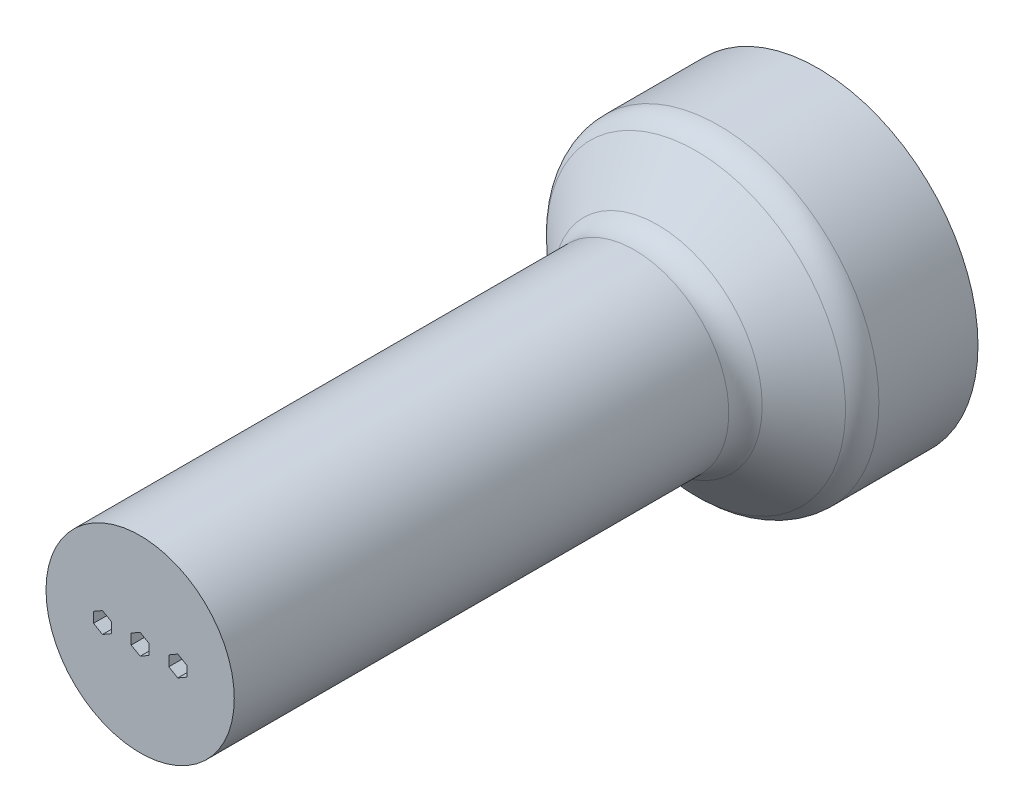
SolidWorks part; units mm, degrees
ref_plane "Front Plane" through (0, 0, 0) normal (0, 0, 1) x (1, 0, 0)
ref_plane "Top Plane" through (0, 0, 0) normal (0, 1, 0) x (1, 0, 0)
ref_plane "Right Plane" through (0, 0, 0) normal (1, 0, 0) x (0, 0, -1)
sketch "Sketch1" plane through (0, 0, 0) normal (0, 0, 1) x (1, 0, 0)
  circle A0 centre (0, 0) radius 25
  dimension "D1" = 50
extrude "Boss-Extrude1" add sketch "Sketch1" along normal blind 150
sketch "Sketch2" plane through (0, 0, 0) normal (0, 0, 1) x (1, 0, 0)
  circle A0 centre (0, 0) radius 42.5
  point P0 (0, 0)
  dimension "D1" = 85
extrude "Boss-Extrude2" add sketch "Sketch2" against normal blind 30 contours A0
sketch "Sketch3" plane through (0, 0, 0) normal (0, 1, 0) x (1, 0, 0)
  line L0 (0, 0) -> (0, -277.5288) construction
  line L1 (25, 0) -> (25, -15)
  line L2 (25, 0) -> (42.5, 0)
  line L3 (42.5, 0) -> (25, -15)
  dimension "D2" = 15
revolve "Revolve1" add sketch "Sketch3" angle 360 about L0
fillet "Fillet4" radius 8 1 edges at (-25, 0, 15)
fillet "Fillet5" radius 8 1 edges at (42.5, 0, 0)
sketch "Sketch4" plane through (0, 0, 0) normal (0, 0, 1) x (1, 0, 0)
  line L0 (0, 0) -> (-67.4265, 0) construction
  line L1 (-67.4265, 0) -> (67.201, 0) construction
  circle A0 centre (0, 0) radius 1.6
  circle A1 centre (-10, 0) radius 1.6
  circle A2 centre (10, 0) radius 1.6
  dimension "D1" = 3.2
  dimension "D2" = 10
  dimension "D3" = 10
extrude "Cut-Extrude1" cut sketch "Sketch4" against normal up to surface (30 mm away) up to face at (42.5, 0, -30)
sketch "Sketch5" plane through (0, 0, 150) normal (0, 0, 1) x (1, 0, 0)
  line L1 (-7.6184, -1.375) -> (-7.6184, 1.375)
  line L2 (-7.6184, 1.375) -> (-10, 2.75)
  line L3 (-10, 2.75) -> (-12.3816, 1.375)
  line L4 (-12.3816, 1.375) -> (-12.3816, -1.375)
  line L5 (-12.3816, -1.375) -> (-10, -2.75)
  line L6 (-10, -2.75) -> (-7.6184, -1.375)
  line L7 (0, -2.75) -> (2.3816, -1.375)
  line L8 (2.3816, -1.375) -> (2.3816, 1.375)
  line L9 (2.3816, 1.375) -> (0, 2.75)
  line L10 (0, 2.75) -> (-2.3816, 1.375)
  line L11 (-2.3816, 1.375) -> (-2.3816, -1.375)
  line L12 (-2.3816, -1.375) -> (0, -2.75)
  line L13 (10, -2.75) -> (12.3816, -1.375)
  line L14 (12.3816, -1.375) -> (12.3816, 1.375)
  line L15 (12.3816, 1.375) -> (10, 2.75)
  line L16 (10, 2.75) -> (7.6184, 1.375)
  line L17 (7.6184, 1.375) -> (7.6184, -1.375)
  line L18 (7.6184, -1.375) -> (10, -2.75)
  circle A0 centre (-10, 0) radius 1.6 construction
  circle A1 centre (0, 0) radius 1.6 construction
  circle A2 centre (10, 0) radius 1.6 construction
  circle A3 centre (-10, 0) radius 1.6
  circle A4 centre (0, 0) radius 1.6
  circle A5 centre (10, 0) radius 1.6
  circle A6 centre (-10, 0) radius 2.75 construction
  circle A7 centre (0, 0) radius 2.75 construction
  circle A8 centre (10, 0) radius 2.75 construction
  dimension "D1" = 5.5
extrude "Cut-Extrude4" cut sketch "Sketch5" against normal blind 155 contours L8 L9 L10 L11 L12 L7 | L14 L15 L16 L17 L18 L13 | L5 L6 L1 L2 L3 L4
sketch "Sketch6" plane through (0, 0, -30) normal (0, 0, -1) x (-1, 0, 0)
  line L0 (-54.0089, 0) -> (51.5283, 0) construction
  line L1 (0, 0) -> (0, 27.5118) construction
  circle A0 centre (0, 0) radius 1.6 construction
  circle A1 centre (10, 0) radius 1.6 construction
  circle A2 centre (-10, 0) radius 1.6 construction
  circle A3 centre (0, 0) radius 1.6
  circle A4 centre (10, 0) radius 1.6
  circle A5 centre (-10, 0) radius 1.6
  circle A6 centre (30, 0) radius 10
  circle A7 centre (-30, 0) radius 10
  dimension "D1" = 20
  dimension "D2" = 20
extrude "Cut-Extrude5" cut sketch "Sketch6" against normal blind 8 contours A7 | A6
